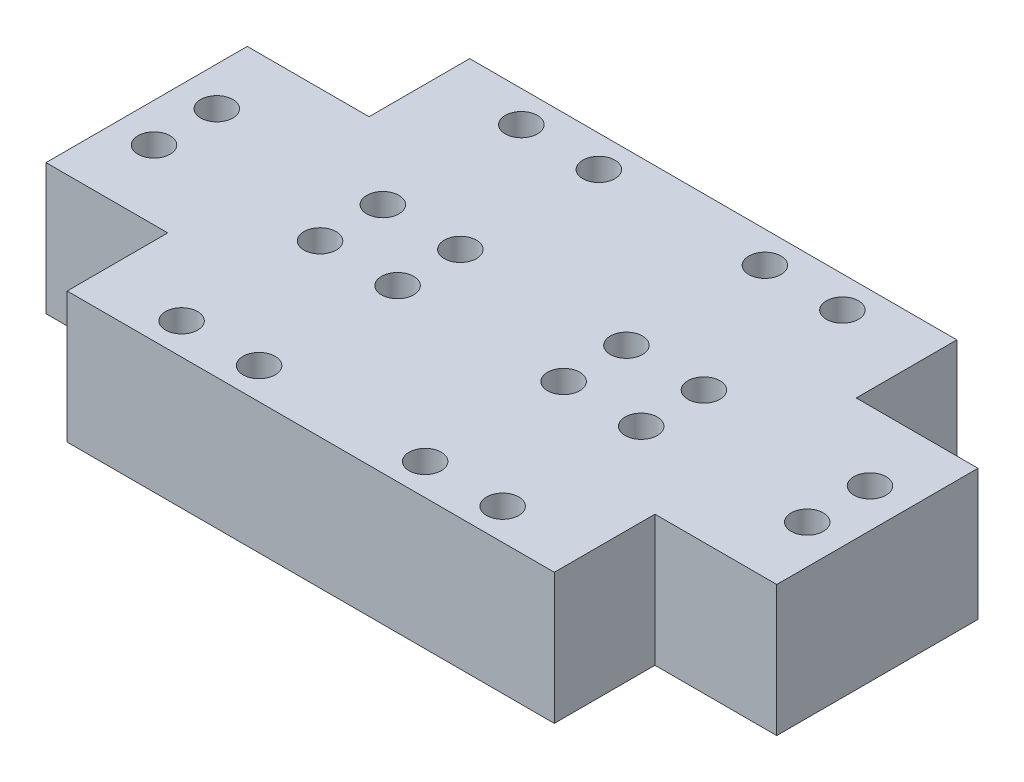
SolidWorks part; units mm, degrees
ref_plane "Front Plane" through (0, 0, 0) normal (0, 0, 1) x (1, 0, 0)
ref_plane "Top Plane" through (0, 0, 0) normal (0, 1, 0) x (1, 0, 0)
ref_plane "Right Plane" through (0, 0, 0) normal (1, 0, 0) x (0, 0, -1)
sketch "Sketch1" plane through (0, 0, 0) normal (0, 1, 0) x (1, 0, 0)
  line L1 (0, 0) -> (9.3045, 0)
  line L2 (0, 0) -> (0, 7.6879)
  line L3 (0, 7.6879) -> (9.3045, 7.6879)
  line L4 (9.3045, 0) -> (9.3045, 7.6879)
  circle A0 centre (6.343, 5.2905) radius 1.2298
extrude "Boss-Extrude1" add sketch "Sketch1" along normal blind 10
mirror "Mirror1" about plane through (0, 10, 0) normal (1, 0, 0) of "Boss-Extrude1"
mirror "Mirror8" about plane through (0, 10, 0) normal (0, 0, -1) of "Boss-Extrude1"
mirror "Mirror9" about plane through (0, 10, -7.6879) normal (0, 0, 1) of "Mirror8"
mirror "Mirror10" about plane through (9.3045, 10, 0) normal (-1, 0, 0) of "Mirror9", "Boss-Extrude1", "Mirror8"
mirror "Mirror11" about plane through (0, 10, -7.6879) normal (0, 0, 1) of bodies 105
mirror "Mirror12"
